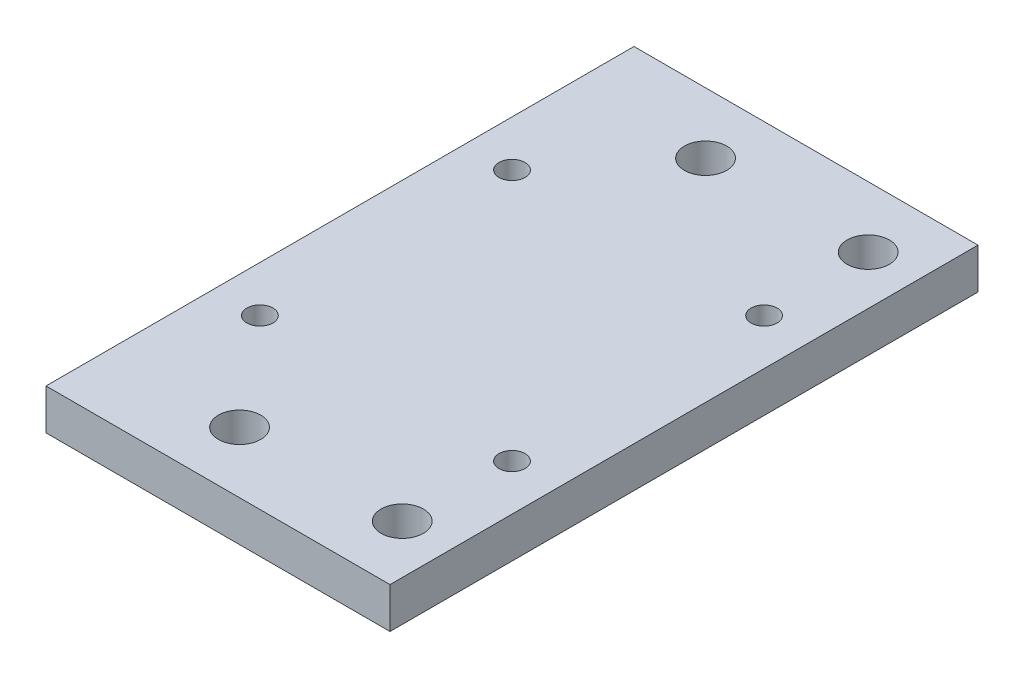
SolidWorks part; units mm, degrees
material "PET"
ref_plane "Front Plane" through (0, 0, 0) normal (0, 0, 1) x (1, 0, 0)
ref_plane "Top Plane" through (0, 0, 0) normal (0, 1, 0) x (1, 0, 0)
ref_plane "Right Plane" through (0, 0, 0) normal (1, 0, 0) x (0, 0, -1)
sketch "Sketch2" plane through (0, 0, 0) normal (0, 1, 0) x (1, 0, 0)
  line L0 (-21.15, 21.15) -> (21.15, -21.15) construction
  line L1 (-21.15, -21.15) -> (21.15, -21.15)
  line L2 (-21.15, -21.15) -> (-21.15, 21.15)
  line L3 (-21.15, 21.15) -> (21.15, 21.15)
  line L4 (21.15, -21.15) -> (21.15, 21.15)
  line L5 (-21.15, 21.15) -> (21.15, 21.15)
  line L6 (-21.15, 21.15) -> (-21.15, 36.15)
  line L7 (-21.15, 36.15) -> (21.15, 36.15)
  line L8 (21.15, 21.15) -> (21.15, 36.15)
  line L9 (21.15, -21.15) -> (-21.15, -21.15)
  line L10 (21.15, -21.15) -> (21.15, -36.15)
  line L11 (21.15, -36.15) -> (-21.15, -36.15)
  line L12 (-21.15, -21.15) -> (-21.15, -36.15)
  line L13 (-21.15, 28.65) -> (21.15, 28.65) construction
  line L14 (-21.15, -28.65) -> (21.15, -28.65) construction
  line L15 (15.5, 15.5) -> (-15.5, -15.5) construction
  circle A0 centre (-4.85, 28.65) radius 2.6
  circle A1 centre (15.15, 28.65) radius 2.6
  circle A2 centre (-4.85, -28.65) radius 2.6
  circle A3 centre (15.15, -28.65) radius 2.6
  circle A4 centre (-15.5, 15.5) radius 1.6
  circle A5 centre (15.5, -15.5) radius 1.6
  circle A6 centre (15.5, 15.5) radius 1.6
  circle A7 centre (-15.5, -15.5) radius 1.6
  dimension "D3" = 5.2
  dimension "D4" = 5.2
  dimension "D9" = 5.2
  dimension "D10" = 5.2
  dimension "D13" = 3.2
  dimension "D14" = 3.2
  dimension "D15" = 3.2
  dimension "D16" = 3.2
  dimension "D1" = 42.3
  dimension "D2" = 42.3
  dimension "D5" = 15
  dimension "D6" = 15
  dimension "D7" = 20
  dimension "D8" = 6
  dimension "D11" = 20
  dimension "D12" = 6
  dimension "D17" = 31
  dimension "D18" = 16.3
extrude "Boss-Extrude1" add sketch "Sketch2" along normal blind 5 contours L1 L4 L3 L2 A7 A6 A5 A4 | L1 L12 L11 L10 A3 A2 | L3 L8 L7 L6 A1 A0
sketch "Sketch3" [suppressed] plane through (0, 5, 0) normal (0, 1, 0) x (1, 0, 0)
  circle A0 centre (-15.5, 15.5) radius 3
  circle A1 centre (15.5, 15.5) radius 3
  circle A2 centre (15.5, -15.5) radius 3
  circle A3 centre (-15.5, -15.5) radius 3
  dimension "D1" = 6
  dimension "D2" = 6
  dimension "D3" = 6
  dimension "D4" = 6
extrude "Cut-Extrude1" [suppressed] cut sketch "Sketch3" against normal blind 3
